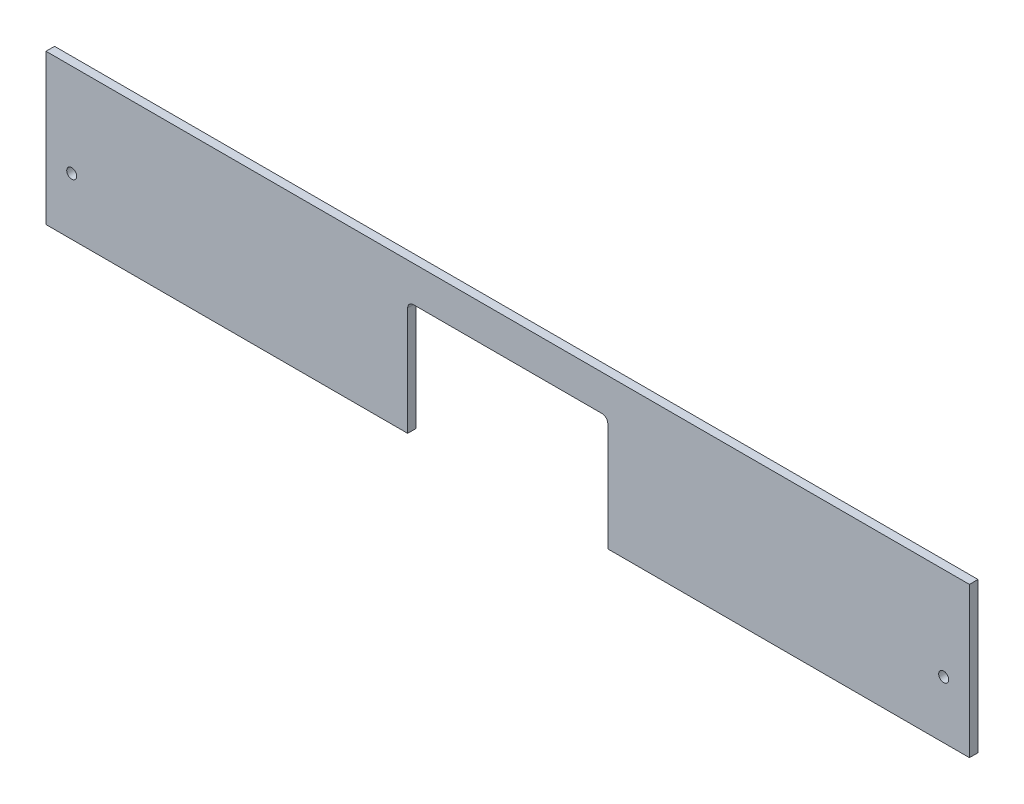
SolidWorks part; units mm, degrees
material "Acrylic (Medium-high impact)"
ref_plane "Front Plane" through (0, 0, 0) normal (0, 0, 1) x (1, 0, 0)
ref_plane "Top Plane" through (0, 0, 0) normal (0, 1, 0) x (1, 0, 0)
ref_plane "Right Plane" through (0, 0, 0) normal (1, 0, 0) x (0, 0, -1)
sketch "Sketch1" plane through (0, 0, 0) normal (0, 0, 1) x (1, 0, 0)
  line L1 (-161.5, 25) -> (161.5, 25)
  line L2 (-161.5, 25) -> (-161.5, -25)
  line L3 (-161.5, -25) -> (161.5, -25)
  line L4 (161.5, 25) -> (161.5, -25)
  line L5 (-161.5, 25) -> (161.5, -25) construction
  line L6 (-161.5, -25) -> (161.5, 25) construction
  point P0 (0, 0)
  dimension "D1" = 50
  dimension "D2" = 323
extrude "Boss-Extrude1" add sketch "Sketch1" along normal blind 3
sketch "Sketch2" plane through (0, 0, 3) normal (0, 0, 1) x (1, 0, 0)
  line L0 (-161.5, -25) -> (161.5, -25) construction
  line L1 (-35, -25) -> (35, -25)
  line L2 (-35, -25) -> (-35, 15)
  line L3 (-35, 15) -> (35, 15)
  line L4 (35, -25) -> (35, 15)
  point P6 (0, 15)
  dimension "D1" = 40
  dimension "D2" = 70
extrude "Cut-Extrude1" cut sketch "Sketch2" against normal through all both and the other way through all
fillet "Fillet1" radius 2 2 edges at (35, 15, 1.5) (-35, 15, 1.5)
sketch "Sketch3" plane through (0, 25, 0) normal (0, 1, 0) x (1, 0, 0)
  line L4 (161.5, 0) -> (-161.5, 0)
  line L5 (-161.5, 0) -> (-161.5, -3)
  line L6 (-161.5, -3) -> (161.5, -3)
  line L7 (161.5, -3) -> (161.5, 0)
  line L8 (161.5, 0) -> (-161.5, 0)
  line L9 (-161.5, 0) -> (-161.5, -3)
  line L10 (-161.5, -3) -> (161.5, -3)
  line L11 (161.5, -3) -> (161.5, 0)
  dimension "D1" = 0
extrude "Boss-Extrude2" add sketch "Sketch3" along normal blind 2.5 contours L8 L9 L10 L11
sketch "Sketch4" plane through (0, 0, 3) normal (0, 0, 1) x (1, 0, 0)
  line L0 (-161.5, -25) -> (-35, -25) construction
  line L1 (-161.5, 27.5) -> (-161.5, -25) construction
  line L2 (0, -25) -> (0, 27.5) construction
  line L3 (-161.5, -25) -> (161.5, -25) construction
  line L4 (-161.5, 27.5) -> (161.5, 27.5) construction
  circle A0 centre (-152.5, -5) radius 1.75
  circle A1 centre (152.5, -5) radius 1.75
  dimension "D1" = 3.5
  dimension "D2" = 20
  dimension "D3" = 9
extrude "Cut-Extrude2" cut sketch "Sketch4" against normal through all
